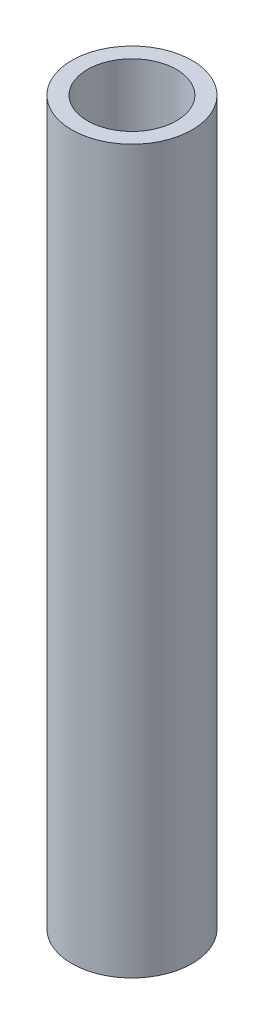
SolidWorks part; units mm, degrees
ref_plane "Front Plane" through (0, 0, 0) normal (0, 0, 1) x (1, 0, 0)
ref_plane "Top Plane" through (0, 0, 0) normal (0, 1, 0) x (1, 0, 0)
ref_plane "Right Plane" through (0, 0, 0) normal (1, 0, 0) x (0, 0, -1)
sketch "Sketch1" plane through (0, 0, 0) normal (0, 1, 0) x (1, 0, 0)
  circle A0 centre (0, 0) radius 6.35
  circle A1 centre (0, 0) radius 4.699
extrude "Boss-Extrude1" add sketch "Sketch1" along normal blind 76.2
